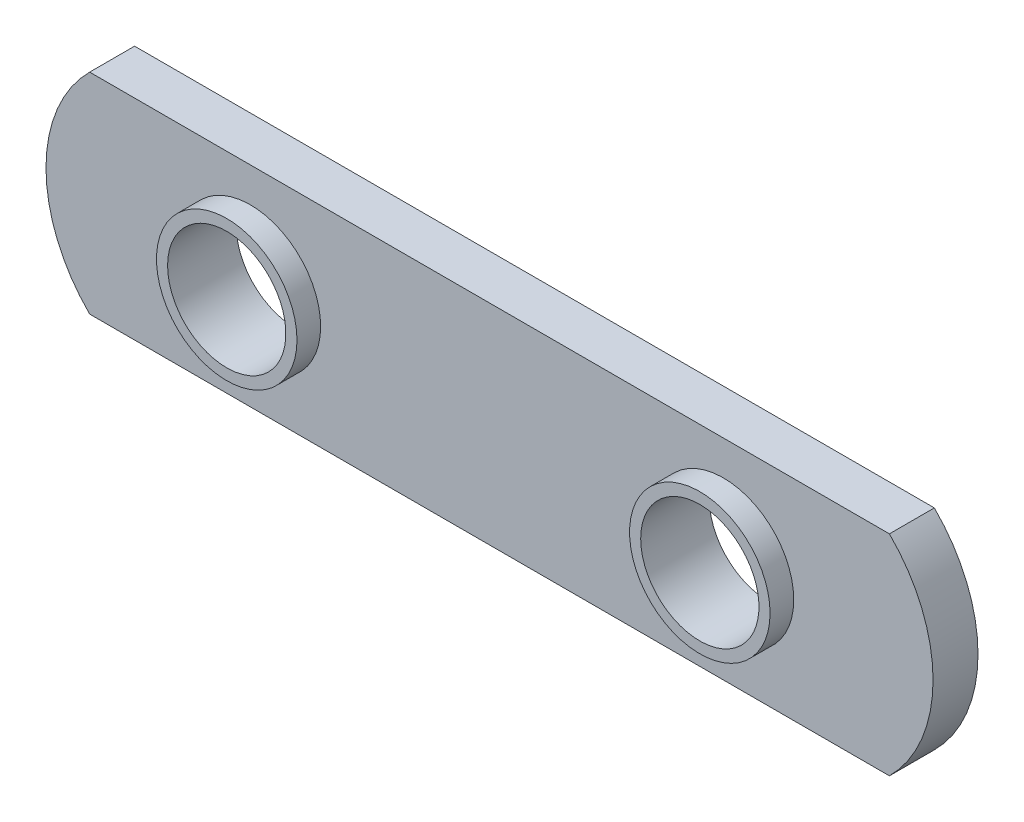
SolidWorks part; units mm, degrees
material "AISI 1020"
ref_plane "Front Plane" through (0, 0, 0) normal (0, 0, 1) x (1, 0, 0)
ref_plane "Top Plane" through (0, 0, 0) normal (0, 1, 0) x (1, 0, 0)
ref_plane "Right Plane" through (0, 0, 0) normal (1, 0, 0) x (0, 0, -1)
sketch "Sketch1" plane through (0, 0, 0) normal (0, 0, 1) x (1, 0, 0)
  line L0 (99.423, 128.4713) -> (147.048, 128.4713) construction
  line L88 (101.7666, 134.0974) -> (144.7043, 134.0974)
  line L89 (101.7666, 122.8452) -> (144.7043, 122.8452)
  arc A3 (101.7666, 134.0974) -> (101.7666, 122.8452) centre (107.3478, 128.4713) ccw
  arc A4 (144.7043, 122.8452) -> (144.7043, 134.0974) centre (139.1232, 128.4713) ccw
  dimension "D1" = 47.625
  dimension "D3" = 7.9248
  dimension "D2" = 11.2522
extrude "Extrude1" add sketch "Sketch1" along normal blind 2.413
sketch "Sketch4" plane through (0, 0, 2.413) normal (0, 0, 1) x (1, 0, 0)
  line L0 (99.423, 128.4713) -> (147.048, 128.4713) construction
  circle A0 centre (135.7958, 128.4713) radius 3.7719
  arc A1 (101.7666, 134.0974) -> (101.7666, 122.8452) centre (107.3478, 128.4713) ccw construction
  arc A2 (144.7043, 122.8452) -> (144.7043, 134.0974) centre (139.1232, 128.4713) ccw construction
  circle A3 centre (110.3958, 128.4713) radius 3.7719
  dimension "D1" = 7.5438
  dimension "D4" = 10.9728
  dimension "D2" = 11.2522
  dimension "D3" = 25.4
extrude "Extrude3" add sketch "Sketch4" along normal blind 1.27
sketch "Sketch6" plane through (0, 0, 0) normal (0, 0, -1) x (-1, 0, 0)
  circle A0 centre (-135.7958, 128.4713) radius 3.175
  circle A1 centre (-110.3958, 128.4713) radius 3.175
  dimension "D1" = 6.35
extrude "Cut-Extrude1" cut sketch "Sketch6" against normal through all
